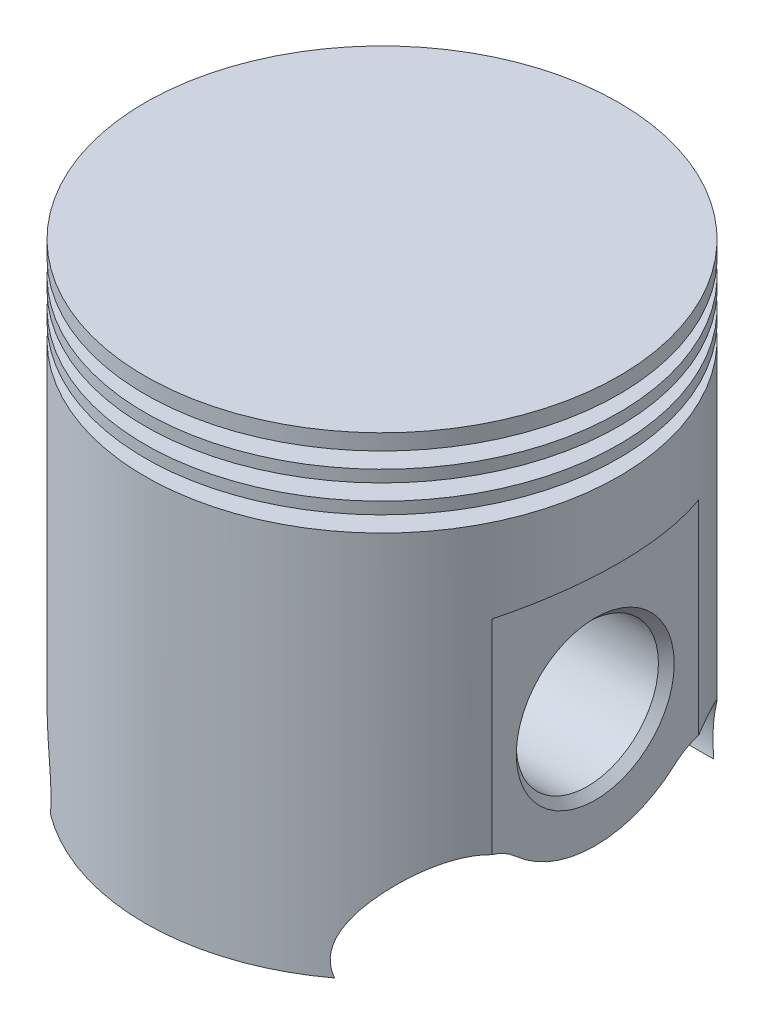
SolidWorks part; units mm, degrees
ref_plane "Front Plane" through (0, 0, 0) normal (0, 0, 1) x (1, 0, 0)
ref_plane "Top Plane" through (0, 0, 0) normal (0, 1, 0) x (1, 0, 0)
ref_plane "Right Plane" through (0, 0, 0) normal (1, 0, 0) x (0, 0, -1)
sketch "Sketch1" plane through (0, 0, 0) normal (1, 0, 0) x (0, 0, -1)
  line L0 (0, 0) -> (30, 0)
  line L1 (30, 0) -> (30, -2)
  line L2 (30, -60) -> (26, -60)
  line L3 (26, -60) -> (26, -54)
  line L4 (26, -54) -> (22.0206, -50.6609)
  line L5 (22.0206, -40.6609) -> (24, -39)
  line L6 (22.0206, -50.6609) -> (22.0206, -40.6609)
  line L7 (24, -39) -> (24, -7.5)
  line L8 (30, -4) -> (30, -5.5)
  line L9 (24, -7.5) -> (0, -7.5)
  line L10 (0, -7.5) -> (0, 0)
  line L11 (30, -2) -> (25.52, -2)
  line L12 (30, -7.5) -> (30, -9)
  line L13 (30, -4) -> (25.52, -4)
  line L14 (25.52, -2) -> (25.52, -4)
  line L15 (30, -5.5) -> (25.52, -5.5)
  line L16 (30, -11) -> (30, -60)
  line L17 (30, -7.5) -> (25.52, -7.5)
  line L18 (25.52, -5.5) -> (25.52, -7.5)
  line L19 (30, -9) -> (25.52, -9)
  line L21 (30, -11) -> (25.52, -11)
  line L22 (25.52, -9) -> (25.52, -11)
  point P7 (15, 0)
  dimension "D1" = 30
  dimension "D2" = 60
  dimension "D3" = 4
  dimension "D4" = 6
  dimension "D5" = 130
  dimension "D6" = 130
  dimension "D7" = 10
  dimension "D8" = 6
  dimension "D9" = 15
  dimension "D10" = 7.5
  dimension "D11" = 2
  dimension "D12" = 2
  dimension "D13" = 1.5
  dimension "D14" = 1.5
  dimension "D15" = 25.52
revolve "Revolve1" add sketch "Sketch1" angle 360 about L10
ref_plane "Plane1" through (10, 0, 0) normal (1, 0, 0) x (0, 0, -1)
sketch "Sketch2" plane through (10, 0, 0) normal (1, 0, 0) x (0, 0, -1)
  circle A0 centre (0, -38) radius 12.5
  point P2 (0, 0)
  dimension "D1" = 25
  dimension "D2" = 38
extrude "Boss-Extrude1" add sketch "Sketch2" along normal up to surface (17.2718 mm away)
mirror "Mirror1" about plane through (0, 0, 0) normal (1, 0, 0) of "Boss-Extrude1"
sketch "Sketch3" plane through (0, 0, 0) normal (1, 0, 0) x (0, 0, -1)
  circle A0 centre (0, -38) radius 9
  dimension "D1" = 18
extrude "Cut-Extrude1" cut sketch "Sketch3" against normal mid plane 113
ref_plane "Plane2" through (30, 0, 0) normal (1, 0, 0) x (0, 0, -1)
sketch "Sketch4" plane through (30, 0, 0) normal (1, 0, 0) x (0, 0, -1)
  line L1 (-17.5, -20.5) -> (17.5, -20.5)
  line L2 (-17.5, -20.5) -> (-17.5, -55.5)
  line L3 (-17.5, -55.5) -> (17.5, -55.5)
  line L4 (17.5, -20.5) -> (17.5, -55.5)
  line L5 (-17.5, -20.5) -> (17.5, -55.5) construction
  line L6 (-17.5, -55.5) -> (17.5, -20.5) construction
  point P0 (0, -38)
  dimension "D1" = 35
  dimension "D2" = 35
extrude "Cut-Extrude3" cut sketch "Sketch4" against normal blind 3 draft 20
mirror "Mirror2" about plane through (0, 0, 0) normal (1, 0, 0) of "Cut-Extrude3"
chamfer "Chamfer1" distance 1 angle 45 2 edges at (-27, -38, 9) (27, -38, -9)
sketch "Sketch5" plane through (0, 0, 0) normal (1, 0, 0) x (0, 0, -1)
  line L0 (-30, -60) -> (30, -60) construction
  line L1 (0, -38) -> (0, -66.8721) construction
  line L2 (-24, -60) -> (24, -60)
  arc A0 (10, -49.1803) -> (-10, -49.1803) centre (0, -38) cw
  spline S0 degree 3 poles (10, -49.1803) (16.9907, -42.9277) (25.8093, -52.9215) (24, -60) knots 0 0 0 0 1 1 1 1
  spline S1 degree 3 poles (-10, -49.1803) (-16.9907, -42.9277) (-25.8093, -52.9215) (-24, -60) knots 0 0 0 0 1 1 1 1
  dimension "D1" = 15
  dimension "D4" = 12
  dimension "D2" = 20
  dimension "D3" = 6
  dimension "D5" = 12
extrude "Cut-Extrude4" cut sketch "Sketch5" against normal mid plane 112
